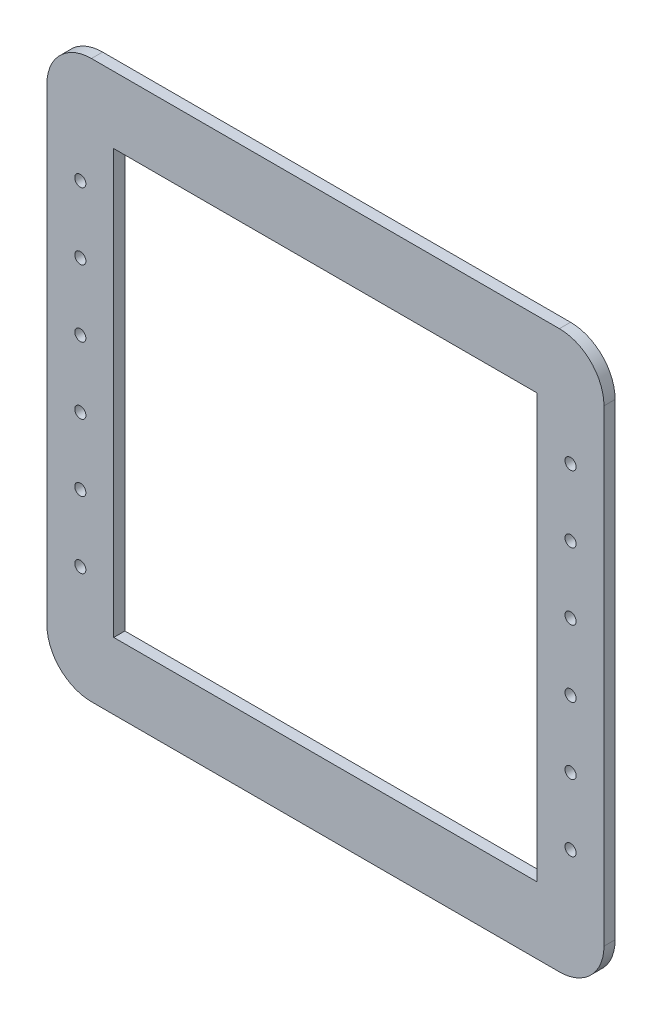
SolidWorks part; units mm, degrees
ref_plane "Front Plane" through (0, 0, 0) normal (0, 0, 1) x (1, 0, 0)
ref_plane "Top Plane" through (0, 0, 0) normal (0, 1, 0) x (1, 0, 0)
ref_plane "Right Plane" through (0, 0, 0) normal (1, 0, 0) x (0, 0, -1)
sketch "Sketch1" plane through (0, 0, 0) normal (0, 0, 1) x (1, 0, 0)
  line L0 (-95, 95) -> (-95, -95)
  line L1 (-105, 125) -> (105, 125)
  line L2 (-125, 105) -> (-125, -105)
  line L3 (-105, -125) -> (105, -125)
  line L4 (125, 105) -> (125, -105)
  line L5 (-125, 125) -> (125, -125) construction
  line L6 (-125, -125) -> (125, 125) construction
  line L7 (-95, -95) -> (95, -95)
  line L8 (95, 95) -> (95, -95)
  line L9 (-95, 95) -> (95, 95)
  arc A0 (-125, -105) -> (-105, -125) centre (-105, -105) ccw
  arc A1 (105, -125) -> (125, -105) centre (105, -105) ccw
  arc A2 (105, 125) -> (125, 105) centre (105, 105) cw
  arc A3 (-105, 125) -> (-125, 105) centre (-105, 105) ccw
  arc A4 (-95, -95) -> (-95, -95) centre (-95, -95) ccw
  arc A5 (95, -95) -> (95, -95) centre (95, -95) ccw
  arc A6 (95, 95) -> (95, 95) centre (95, 95) cw
  arc A7 (-95, 95) -> (-95, 95) centre (-95, 95) ccw
  point P0 (0, 0)
  dimension "D2" = 20
  dimension "D1" = 250
  dimension "D3" = 30
extrude "Boss-Extrude1" add sketch "Sketch1" along normal blind 5
sketch "Sketch2" plane through (0, 0, 5) normal (0, 0, 1) x (1, 0, 0)
  line L1 (-110, 75) -> (110, 75) construction
  line L2 (-110, 75) -> (-110, -75) construction
  line L3 (-110, -75) -> (110, -75) construction
  line L4 (110, 75) -> (110, -75) construction
  line L5 (-110, 75) -> (110, -75) construction
  line L6 (-110, -75) -> (110, 75) construction
  circle A0 centre (-110, 75) radius 2.5
  circle A1 centre (110, 75) radius 2.5
  point P0 (0, 0)
  point P11 (-110, 73.5825)
  dimension "D3" = 5
  dimension "D1" = 220
  dimension "D2" = 150
extrude "Cut-Extrude1" cut sketch "Sketch2" against normal through all
pattern_linear "LPattern1" count 6 spacing 30 along (0, -1, 0) of "Cut-Extrude1"
